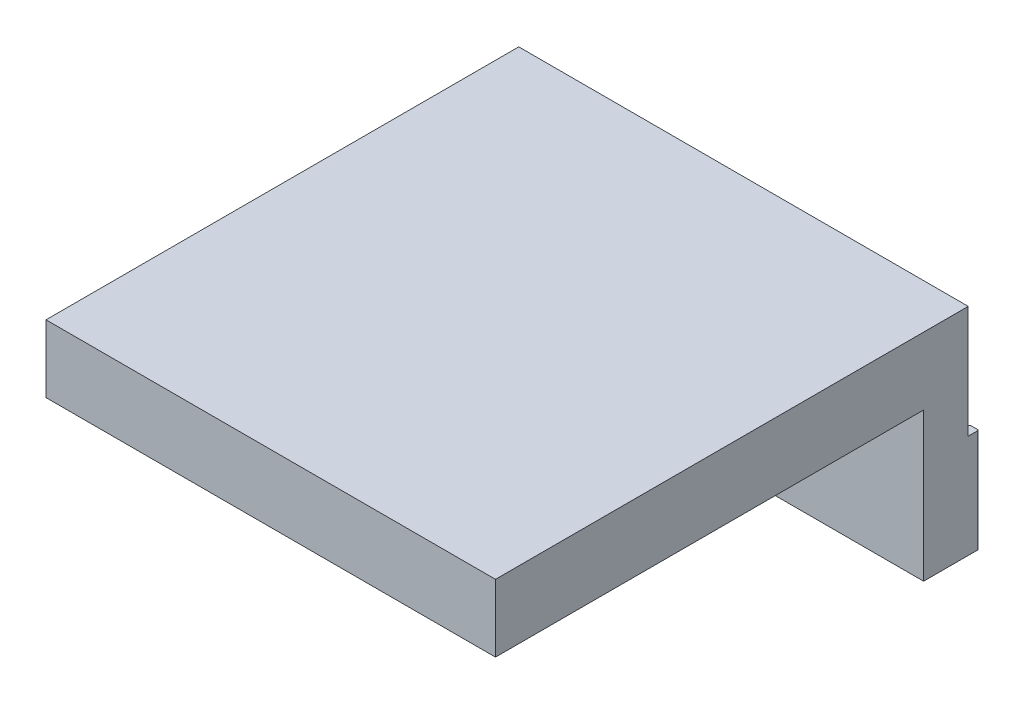
SolidWorks part; units mm, degrees
other "Câmera1"
ref_plane "Plano frontal" through (0, 0, 0) normal (0, 0, 1) x (1, 0, 0)
ref_plane "Plano superior" through (0, 0, 0) normal (0, 1, 0) x (1, 0, 0)
ref_plane "Plano direito" through (0, 0, 0) normal (1, 0, 0) x (0, 0, -1)
sketch "Esboço4" plane through (0, 0, 0) normal (0, 1, 0) x (1, 0, 0)
  line L0 (-19.2, 2.35) -> (-19.2, 1.65)
  line L1 (-20, -2.45) -> (20, -2.45)
  line L2 (-20, -2.45) -> (-20, 2.35)
  line L3 (-19.9, 2.45) -> (-19.3, 2.45)
  line L4 (20, -2.45) -> (20, 2.35)
  line L5 (-19.1, 1.55) -> (-18.1, 1.55)
  line L6 (19.2, 2.35) -> (19.2, 1.65)
  line L7 (19.3, 2.45) -> (19.9, 2.45)
  line L8 (-18, 1.65) -> (-18, 2.35)
  line L9 (-17.9, 2.45) -> (-17.3, 2.45)
  line L10 (-17.2, 2.35) -> (-17.2, 1.65)
  line L11 (-16, 1.65) -> (-16, 2.35)
  line L12 (-15.9, 2.45) -> (-15.3, 2.45)
  line L13 (-15.2, 2.35) -> (-15.2, 1.65)
  line L14 (-14, 1.65) -> (-14, 2.35)
  line L15 (-13.9, 2.45) -> (-13.3, 2.45)
  line L16 (-13.2, 2.35) -> (-13.2, 1.65)
  line L17 (-12, 1.65) -> (-12, 2.35)
  line L18 (-11.9, 2.45) -> (-11.3, 2.45)
  line L19 (-11.2, 2.35) -> (-11.2, 1.65)
  line L20 (-10, 1.65) -> (-10, 2.35)
  line L21 (-9.9, 2.45) -> (-9.3, 2.45)
  line L22 (-9.2, 2.35) -> (-9.2, 1.65)
  line L23 (-8, 1.65) -> (-8, 2.35)
  line L24 (-7.9, 2.45) -> (-7.3, 2.45)
  line L25 (-7.2, 2.35) -> (-7.2, 1.65)
  line L26 (-7.1, 1.55) -> (7.1, 1.55)
  line L27 (-9.1, 1.55) -> (-8.1, 1.55)
  line L28 (-11.1, 1.55) -> (-10.1, 1.55)
  line L29 (-13.1, 1.55) -> (-12.1, 1.55)
  line L30 (-15.1, 1.55) -> (-14.1, 1.55)
  line L31 (-17.1, 1.55) -> (-16.1, 1.55)
  line L32 (17.2, 2.35) -> (17.2, 1.65)
  line L33 (17.3, 2.45) -> (17.9, 2.45)
  line L34 (18, 1.65) -> (18, 2.35)
  line L35 (15.2, 2.35) -> (15.2, 1.65)
  line L36 (15.3, 2.45) -> (15.9, 2.45)
  line L37 (16, 1.65) -> (16, 2.35)
  line L38 (13.2, 2.35) -> (13.2, 1.65)
  line L39 (13.3, 2.45) -> (13.9, 2.45)
  line L40 (14, 1.65) -> (14, 2.35)
  line L41 (11.2, 2.35) -> (11.2, 1.65)
  line L42 (11.3, 2.45) -> (11.9, 2.45)
  line L43 (12, 1.65) -> (12, 2.35)
  line L44 (9.2, 2.35) -> (9.2, 1.65)
  line L45 (9.3, 2.45) -> (9.9, 2.45)
  line L46 (10, 1.65) -> (10, 2.35)
  line L47 (7.2, 2.35) -> (7.2, 1.65)
  line L48 (7.3, 2.45) -> (7.9, 2.45)
  line L49 (8, 1.65) -> (8, 2.35)
  line L50 (8.1, 1.55) -> (9.1, 1.55)
  line L51 (10.1, 1.55) -> (11.1, 1.55)
  line L52 (12.1, 1.55) -> (13.1, 1.55)
  line L53 (14.1, 1.55) -> (15.1, 1.55)
  line L54 (16.1, 1.55) -> (17.1, 1.55)
  line L55 (18.1, 1.55) -> (19.1, 1.55)
  arc A0 (19.9, 2.45) -> (20, 2.35) centre (19.9, 2.35) cw
  arc A1 (19.2, 2.35) -> (19.3, 2.45) centre (19.3, 2.35) cw
  arc A2 (19.1, 1.55) -> (19.2, 1.65) centre (19.1, 1.65) ccw
  arc A3 (18.1, 1.55) -> (18, 1.65) centre (18.1, 1.65) cw
  arc A4 (17.9, 2.45) -> (18, 2.35) centre (17.9, 2.35) cw
  arc A5 (17.2, 2.35) -> (17.3, 2.45) centre (17.3, 2.35) cw
  arc A6 (17.2, 1.65) -> (17.1, 1.55) centre (17.1, 1.65) cw
  arc A7 (16.1, 1.55) -> (16, 1.65) centre (16.1, 1.65) cw
  arc A8 (15.9, 2.45) -> (16, 2.35) centre (15.9, 2.35) cw
  arc A9 (15.2, 2.35) -> (15.3, 2.45) centre (15.3, 2.35) cw
  arc A10 (15.2, 1.65) -> (15.1, 1.55) centre (15.1, 1.65) cw
  arc A11 (14, 1.65) -> (14.1, 1.55) centre (14.1, 1.65) ccw
  arc A12 (13.9, 2.45) -> (14, 2.35) centre (13.9, 2.35) cw
  arc A13 (13.2, 2.35) -> (13.3, 2.45) centre (13.3, 2.35) cw
  arc A14 (13.2, 1.65) -> (13.1, 1.55) centre (13.1, 1.65) cw
  arc A15 (12, 1.65) -> (12.1, 1.55) centre (12.1, 1.65) ccw
  arc A16 (11.9, 2.45) -> (12, 2.35) centre (11.9, 2.35) cw
  arc A17 (11.2, 2.35) -> (11.3, 2.45) centre (11.3, 2.35) cw
  arc A18 (11.2, 1.65) -> (11.1, 1.55) centre (11.1, 1.65) cw
  arc A19 (10, 1.65) -> (10.1, 1.55) centre (10.1, 1.65) ccw
  arc A20 (9.9, 2.45) -> (10, 2.35) centre (9.9, 2.35) cw
  arc A21 (9.2, 2.35) -> (9.3, 2.45) centre (9.3, 2.35) cw
  arc A22 (9.2, 1.65) -> (9.1, 1.55) centre (9.1, 1.65) cw
  arc A23 (8, 1.65) -> (8.1, 1.55) centre (8.1, 1.65) ccw
  arc A24 (7.9, 2.45) -> (8, 2.35) centre (7.9, 2.35) cw
  arc A25 (7.2, 2.35) -> (7.3, 2.45) centre (7.3, 2.35) cw
  arc A26 (7.2, 1.65) -> (7.1, 1.55) centre (7.1, 1.65) cw
  arc A27 (-7.2, 1.65) -> (-7.1, 1.55) centre (-7.1, 1.65) ccw
  arc A28 (-7.3, 2.45) -> (-7.2, 2.35) centre (-7.3, 2.35) cw
  arc A29 (-8, 1.65) -> (-8.1, 1.55) centre (-8.1, 1.65) cw
  arc A30 (-8, 2.35) -> (-7.9, 2.45) centre (-7.9, 2.35) cw
  arc A31 (-9.2, 1.65) -> (-9.1, 1.55) centre (-9.1, 1.65) ccw
  arc A32 (-9.3, 2.45) -> (-9.2, 2.35) centre (-9.3, 2.35) cw
  arc A33 (-10, 2.35) -> (-9.9, 2.45) centre (-9.9, 2.35) cw
  arc A34 (-10, 1.65) -> (-10.1, 1.55) centre (-10.1, 1.65) cw
  arc A35 (-11.2, 1.65) -> (-11.1, 1.55) centre (-11.1, 1.65) ccw
  arc A36 (-11.3, 2.45) -> (-11.2, 2.35) centre (-11.3, 2.35) cw
  arc A37 (-12, 1.65) -> (-12.1, 1.55) centre (-12.1, 1.65) cw
  arc A38 (-12, 2.35) -> (-11.9, 2.45) centre (-11.9, 2.35) cw
  arc A39 (-13.2, 1.65) -> (-13.1, 1.55) centre (-13.1, 1.65) ccw
  arc A40 (-13.3, 2.45) -> (-13.2, 2.35) centre (-13.3, 2.35) cw
  arc A41 (-14, 1.65) -> (-14.1, 1.55) centre (-14.1, 1.65) cw
  arc A42 (-14, 2.35) -> (-13.9, 2.45) centre (-13.9, 2.35) cw
  arc A43 (-15.2, 1.65) -> (-15.1, 1.55) centre (-15.1, 1.65) ccw
  arc A44 (-15.3, 2.45) -> (-15.2, 2.35) centre (-15.3, 2.35) cw
  arc A45 (-16, 1.65) -> (-16.1, 1.55) centre (-16.1, 1.65) cw
  arc A46 (-16, 2.35) -> (-15.9, 2.45) centre (-15.9, 2.35) cw
  arc A47 (-17.2, 1.65) -> (-17.1, 1.55) centre (-17.1, 1.65) ccw
  arc A48 (-17.3, 2.45) -> (-17.2, 2.35) centre (-17.3, 2.35) cw
  arc A49 (-18, 1.65) -> (-18.1, 1.55) centre (-18.1, 1.65) cw
  arc A50 (-18, 2.35) -> (-17.9, 2.45) centre (-17.9, 2.35) cw
  arc A51 (-19.2, 1.65) -> (-19.1, 1.55) centre (-19.1, 1.65) ccw
  arc A52 (-19.2, 2.35) -> (-19.3, 2.45) centre (-19.3, 2.35) ccw
  arc A53 (-20, 2.35) -> (-19.9, 2.45) centre (-19.9, 2.35) cw
  point P0 (0, 0)
  point P62 (19.2, 2.45)
  point P83 (14, 1.55)
  point P92 (12, 1.55)
  point P101 (10, 1.55)
  point P110 (8, 1.55)
  dimension "D2" = 0.1
  dimension "D1" = 7
  dimension "D3" = 14.2
extrude "Ressalto-extrusão2" add sketch "Esboço4" along normal blind 9.2
sketch "Esboço5" plane through (0, 0, -1.55) normal (0, 0, -1) x (-1, 0, 0)
  circle A0 centre (0, 4.6) radius 2.15
  dimension "D1" = 4.3
extrude "Corte-extrusão2" cut sketch "Esboço5" against normal blind 9.2
chamfer "Chanfro2" distance 0.3 angle 45 1 edges at (-2.15, 4.6, -1.55)
sketch "Sketch1" plane through (0, 9.2, 0) normal (0, 1, 0) x (1, 0, 0)
  line L0 (20, -2.45) -> (20, 2.35) construction
  line L1 (-20, -2.45) -> (20, -2.45)
  line L2 (-20, -2.45) -> (-20, 1.5223)
  line L3 (-20, 1.5223) -> (20, 1.5223)
  line L4 (20, -2.45) -> (20, 1.5223)
extrude "Boss-Extrude1" add sketch "Sketch1" along normal blind 10
sketch "Sketch2" plane through (0, 0, 2.45) normal (0, 0, 1) x (1, 0, 0)
  line L0 (20, 19.2) -> (20, 0) construction
  line L1 (-20, 19.2) -> (20, 19.2)
  line L2 (-20, 19.2) -> (-20, 13.2)
  line L3 (-20, 13.2) -> (20, 13.2)
  line L4 (20, 19.2) -> (20, 13.2)
  dimension "D1" = 6
extrude "Boss-Extrude2" add sketch "Sketch2" along normal blind 38.1
